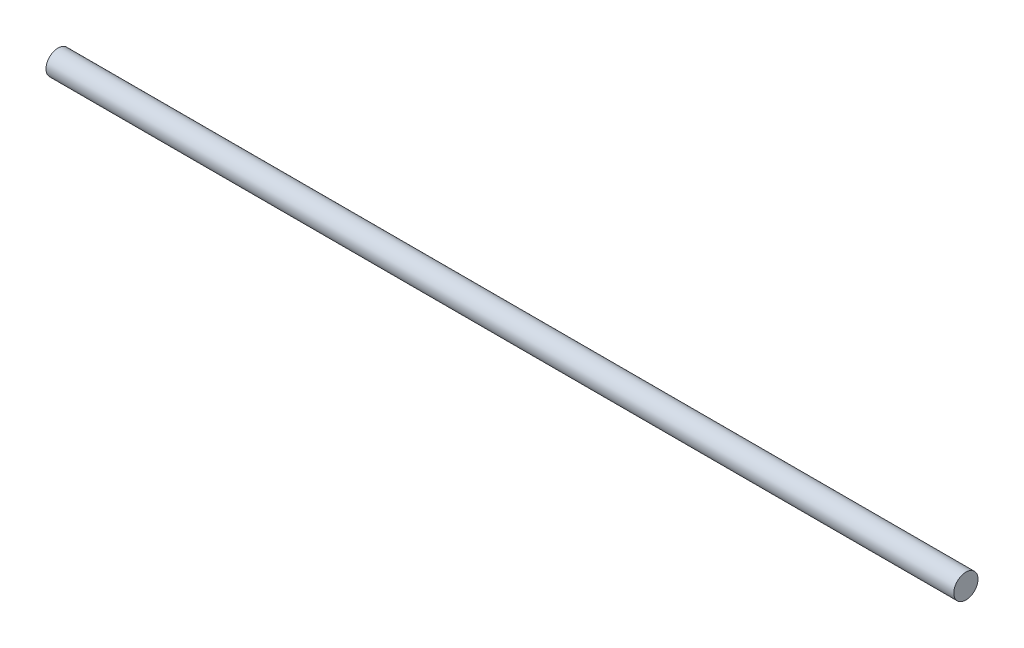
SolidWorks part; units mm, degrees
ref_plane "Front Plane" through (0, 0, 0) normal (0, 0, 1) x (1, 0, 0)
ref_plane "Top Plane" through (0, 0, 0) normal (0, 1, 0) x (1, 0, 0)
ref_plane "Right Plane" through (0, 0, 0) normal (1, 0, 0) x (0, 0, -1)
sketch "Sketch1" plane through (0, 0, 0) normal (1, 0, 0) x (0, 0, -1)
  circle A0 centre (0, 0) radius 8
  dimension "D1" = 16
extrude "Boss-Extrude1" add sketch "Sketch1" along normal blind 600
